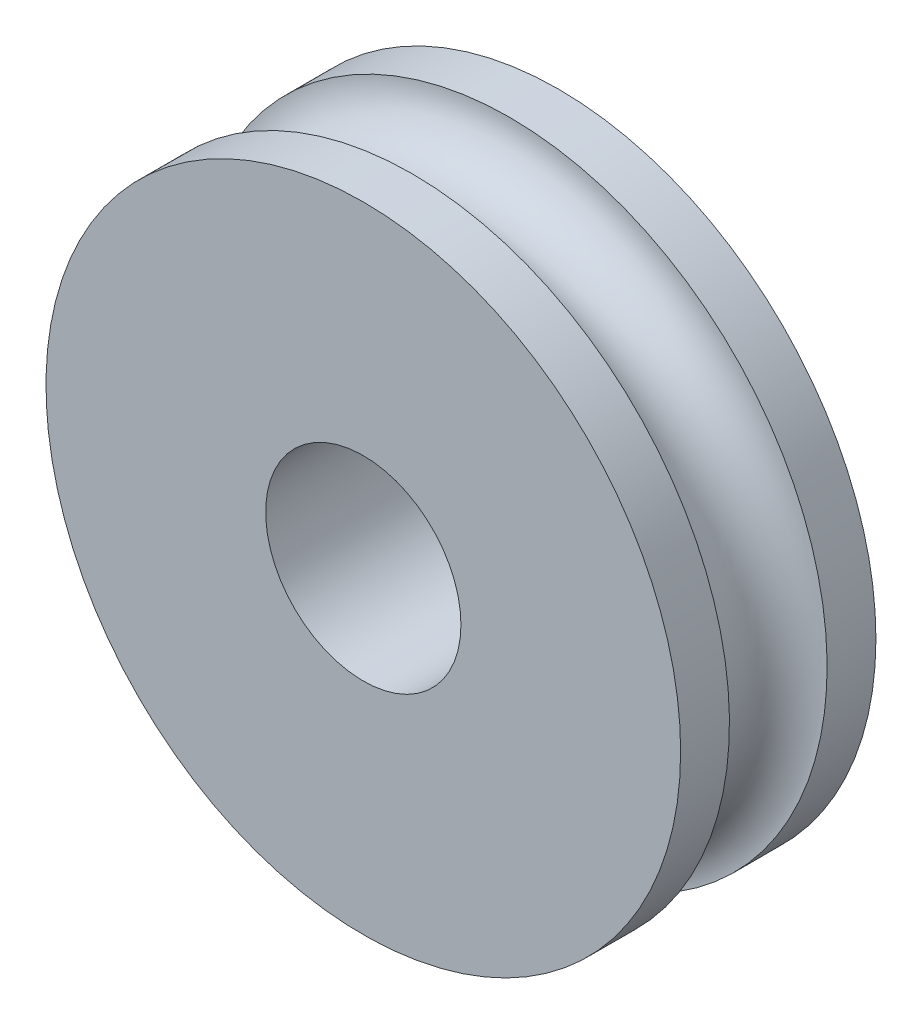
SolidWorks part; units mm, degrees
material "1.0037 (S235JR)"
ref_plane "Front Plane" through (0, 0, 0) normal (0, 0, 1) x (1, 0, 0)
ref_plane "Top Plane" through (0, 0, 0) normal (0, 1, 0) x (1, 0, 0)
ref_plane "Right Plane" through (0, 0, 0) normal (1, 0, 0) x (0, 0, -1)
sketch "Sketch1" plane through (0, 0, 0) normal (0, 0, 1) x (1, 0, 0)
  circle A0 centre (0, 0) radius 6.5
  dimension "D1" = 13
extrude "Boss-Extrude1" add sketch "Sketch1" along normal blind 4
sketch "Sketch2" plane through (0, 0, 4) normal (0, 0, 1) x (1, 0, 0)
  circle A0 centre (0, 0) radius 2
  dimension "D1" = 4
extrude "Cut-Extrude1" cut sketch "Sketch2" against normal through all
ref_plane "Plane1" through (0, 0, 2) normal (0, 0, 1) x (1, 0, 0)
sketch "Sketch3" plane through (0, 0, 2) normal (0, 0, 1) x (1, 0, 0)
  circle A0 centre (0, 0) radius 6.5
  dimension "D1" = 13
sketch "Sketch4" plane through (0, 0, 0) normal (1, 0, 0) x (0, 0, -1)
  line L0 (0, 6.5) -> (-4, 6.5) construction
  circle A0 centre (-2, 6.5) radius 1
  dimension "D1" = 2
sweep "Cut-Sweep1" cut profiles "Sketch4" path "Sketch3"
